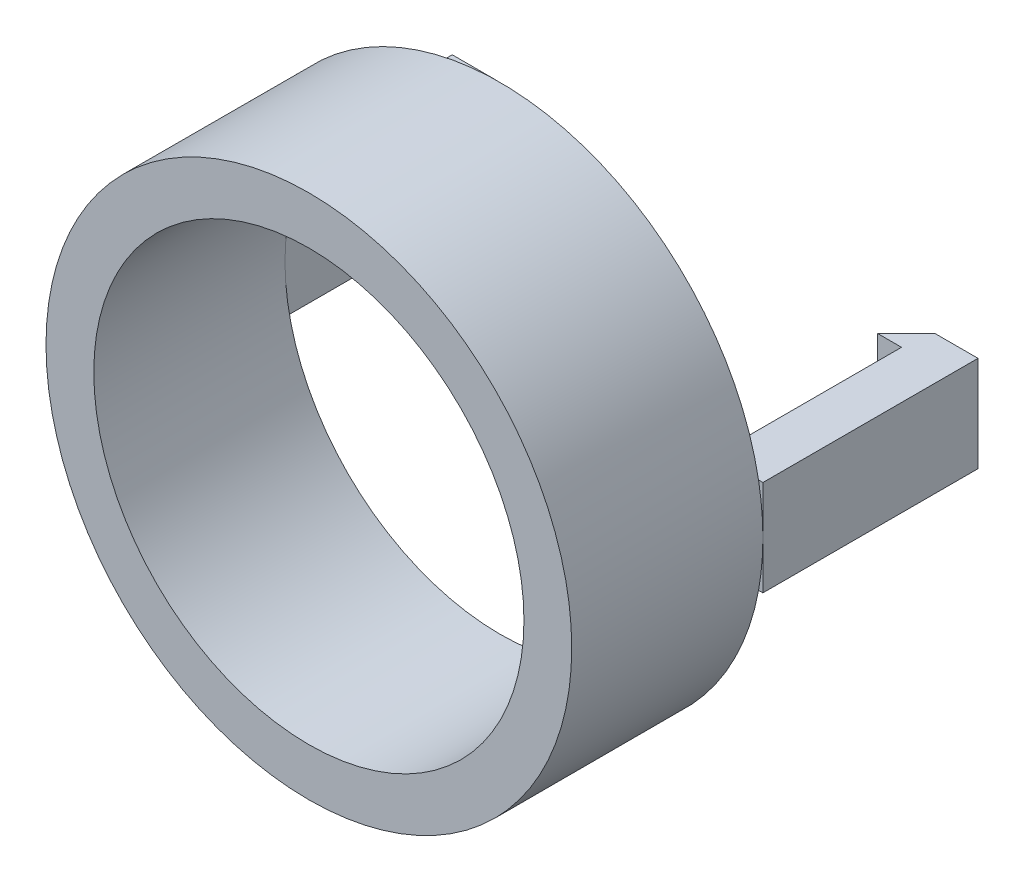
SolidWorks part; units mm, degrees
ref_plane "Front Plane" through (0, 0, 0) normal (0, 0, 1) x (1, 0, 0)
ref_plane "Top Plane" through (0, 0, 0) normal (0, 1, 0) x (1, 0, 0)
ref_plane "Right Plane" through (0, 0, 0) normal (1, 0, 0) x (0, 0, -1)
sketch "Sketch1" plane through (0, 0, 0) normal (0, 0, 1) x (1, 0, 0)
  circle A0 centre (0, 0) radius 9
  circle A1 centre (0, 0) radius 11
  dimension "D1" = 18
  dimension "D2" = 22
extrude "Boss-Extrude1" add sketch "Sketch1" along normal blind 8
sketch "Sketch2" plane through (0, 0, 0) normal (0, 1, 0) x (1, 0, 0)
  line L0 (-11, 0) -> (-11, 9)
  line L1 (-11, 9) -> (-9.2, 9)
  line L2 (-9.2, 9) -> (-8, 7.8)
  line L3 (-8, 7.8) -> (-9, 7.8)
  line L4 (-9, 7.8) -> (-9, 0)
  line L5 (9, 0) -> (-9, 0) construction
  line L6 (-9, 0) -> (-11, 0)
  line L7 (0, -4.4) -> (0, 4.4) construction
  line L8 (9, 0) -> (11, 0)
  line L9 (9, 7.8) -> (9, 0)
  line L10 (8, 7.8) -> (9, 7.8)
  line L11 (9.2, 9) -> (8, 7.8)
  line L12 (11, 9) -> (9.2, 9)
  line L13 (11, 0) -> (11, 9)
  dimension "D1" = 2
  dimension "D2" = 45
  dimension "D3" = 7.8
  dimension "D4" = 9
  dimension "D5" = 1
extrude "Boss-Extrude2" add sketch "Sketch2" along normal mid plane 4
